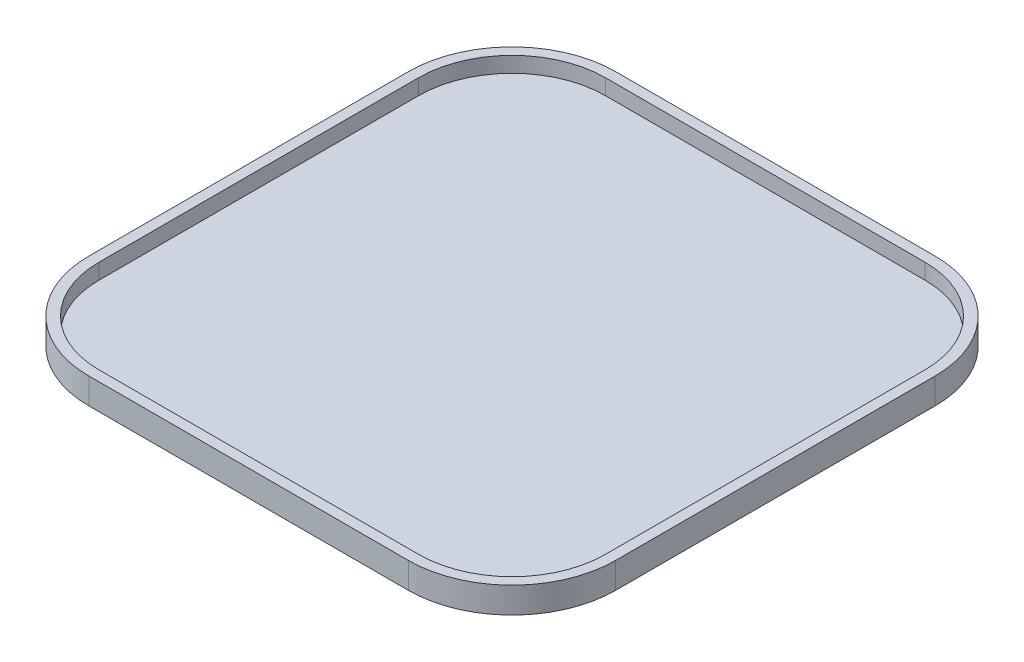
SolidWorks part; units mm, degrees
ref_plane "Front Plane" through (0, 0, 0) normal (0, 0, 1) x (1, 0, 0)
ref_plane "Top Plane" through (0, 0, 0) normal (0, 1, 0) x (1, 0, 0)
ref_plane "Right Plane" through (0, 0, 0) normal (1, 0, 0) x (0, 0, -1)
sketch "Sketch1" plane through (0, 0, 0) normal (0, 1, 0) x (1, 0, 0)
  line L1 (30.8, -50.8) -> (-30.8, -50.8)
  line L2 (50.8, -30.8) -> (50.8, 30.8)
  line L3 (30.8, 50.8) -> (-30.8, 50.8)
  line L4 (-50.8, -30.8) -> (-50.8, 30.8)
  line L5 (50.8, -50.8) -> (-50.8, 50.8) construction
  line L6 (50.8, 50.8) -> (-50.8, -50.8) construction
  arc A0 (30.8, -50.8) -> (50.8, -30.8) centre (30.8, -30.8) ccw
  arc A1 (-30.8, -50.8) -> (-50.8, -30.8) centre (-30.8, -30.8) cw
  arc A2 (50.8, 30.8) -> (30.8, 50.8) centre (30.8, 30.8) ccw
  arc A3 (-30.8, 50.8) -> (-50.8, 30.8) centre (-30.8, 30.8) ccw
  point P0 (0, 0)
  dimension "D2" = 20
  dimension "D1" = 101.6
extrude "Boss-Extrude1" add sketch "Sketch1" along normal blind 5
shell "Shell1" thickness 2
